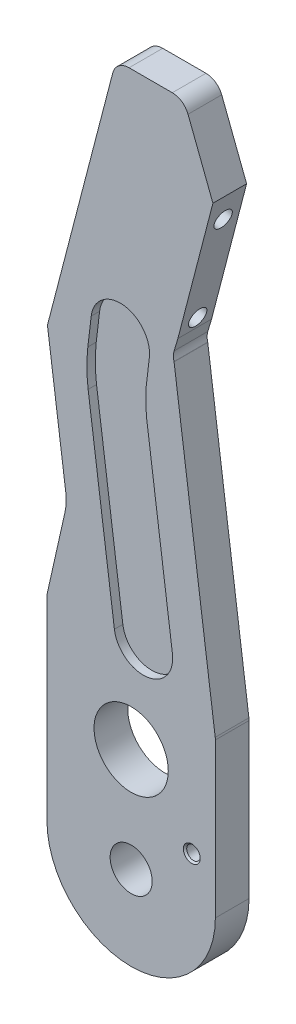
SolidWorks part; units mm, degrees
material "6061-T6 (SS)"
ref_plane "Front Plane" through (0, 0, 0) normal (0, 0, 1) x (1, 0, 0)
ref_plane "Top Plane" through (0, 0, 0) normal (0, 1, 0) x (1, 0, 0)
ref_plane "Right Plane" through (0, 0, 0) normal (1, 0, 0) x (0, 0, -1)
sketch "Sketch1" plane through (0, 0, 0) normal (0, 0, 1) x (1, 0, 0)
  line L0 (-24.2004, 107.4485) -> (-31.75, 73.7706)
  line L2 (-24.2004, 107.4485) -> (-32.7161, 170.4739)
  line L3 (-32.7161, 170.4739) -> (-5.5248, 261.3261)
  line L5 (-31.75, 73.7706) -> (-31.75, 0)
  line L6 (0, 0) -> (0, 372.519) construction
  line L7 (0, 372.519) -> (0, 0) construction
  line L8 (0, 0) -> (0, -96.7447) construction
  line L9 (-31.75, 0) -> (31.75, 0) construction
  line L10 (-108.2097, 215.9) -> (162.3463, 215.9) construction
  line L13 (31.75, 0) -> (31.75, 116.627)
  line L15 (31.9476, 229.9905) -> (19.8752, 261.3261)
  line L16 (19.8752, 261.3261) -> (-5.5248, 261.3261)
  line L17 (31.75, 116.627) -> (15.6763, 175.6244)
  line L18 (15.6763, 175.6244) -> (31.9476, 229.9905)
  arc A0 (-31.75, 0) -> (31.75, 0) centre (0, 0) ccw
  circle A1 centre (0, 0) radius 7.9375
  circle A2 centre (0, 39.116) radius 13.9954
  point P14 (0, -31.75)
  point P23 (-19.1204, 215.9)
  dimension "D1" = 15.875
  dimension "D2" = 27.9908
  dimension "D3" = 31.75
  dimension "D4" = 39.116
  dimension "D5" = 215.9
  dimension "D6" = 94.8339
  dimension "D7" = 25.4
  dimension "D8" = 33.5807
  dimension "D9" = 45.4261
  dimension "D10" = 87.8841
  dimension "D11" = 116.627
  dimension "D12" = 68.1759
  dimension "D13" = 39.8767
  dimension "D14" = 48.3924
  dimension "D15" = 33.6779
  dimension "D16" = 34.5137
extrude "Boss-Extrude1" add sketch "Sketch1" along normal blind 12.7
fillet "Fillet3" radius 19.05 1 edges at (-24.2004, 107.4485, 6.35)
fillet "Fillet1" radius 6.35 7 edges at (-31.75, 73.7706, 6.35) (31.75, 116.627, 6.35) (19.8752, 261.3261, 6.35) (31.9476, 229.9905, 6.35) (-5.5248, 261.3261, 6.35) (-32.7161, 170.4739, 6.35) (15.6763, 175.6244, 6.35)
ref_plane "Plane1" through (0, 261.3261, 0) normal (0, 1, 0) x (1, 0, 0)
ref_plane "Plane2" through (0, 215.9, 0) normal (0, 1, 0) x (1, 0, 0)
ref_plane "Plane3" through (-131.75, 0, 0) normal (-1, 0, 0) x (0, 0, 1)
sketch "Sketch11" plane through (0, 0, 12.7) normal (0, 0, 1) x (1, 0, 0)
  line L0 (-31.75, 7.9375) -> (31.75, 7.9375) construction
  line L1 (-31.75, 73.7706) -> (-31.75, 0) construction
  line L2 (31.75, 0) -> (31.75, 116.627) construction
  line L3 (-31.75, 25.1206) -> (31.75, 25.1206) construction
  line L5 (0, 25.1206) -> (0, 7.9375) construction
  line L7 (-31.75, 16.529) -> (31.75, 16.529) construction
  line L9 (22.86, 25.1206) -> (22.86, 7.9375) construction
  circle A0 centre (0, 0) radius 7.9375 construction
  circle A2 centre (0, 39.116) radius 13.9954 construction
  point P6 (0, 7.9375)
  point P11 (0, 25.1206)
  point P24 (0, 16.529)
  point P30 (22.86, 16.529)
  dimension "D1" = 8.89
hole_wizard "#10 Clearance Hole2" positions "Sketch11" profile "Sketch13" hole size "#10" standard "ANSI Inch" end condition through all
sketch "Sketch13" plane through (22.86, 16.529, 12.7) normal (1, 0, 0) x (0, -1, 0)
  line L0 (0, 0) -> (0, 12.7)
  line L1 (0, 12.7) -> (2.5527, 12.7)
  line L2 (2.5527, 12.7) -> (2.5527, 0.635)
  line L3 (2.5527, 0.635) -> (3.1877, 0)
  line L5 (3.1877, 0) -> (0, 0)
  line L6 (-2.5527, 0.635) -> (-3.1877, 0) construction
  line L11 (0, -6.35) -> (0, 107.95) construction
  dimension "Thru Hole Dia." = 5.1054
  dimension "Thru Hole Depth" = 12.7
  dimension "Near C'Sink Dia." = 6.3754
  dimension "Near C'Sink Angle" = 90
sketch "Sketch15" plane through (-76.8533, 23.0015, 0) normal (-0.958, 0.2867, 0) x (0, 0, 1)
  line L0 (-81.5042, 201.3527) -> (87.1801, 201.3527) construction
sketch "Sketch17" plane through (0, 0, 0) normal (0, 0, -1) x (-1, 0, 0)
  line L0 (-15.9306, 175.6213) -> (-31.75, 58.5394)
  line L1 (-31.75, 0) -> (-31.75, 115.7775) construction
  line L2 (32.5326, 169.1159) -> (24.6578, 110.8333) construction
  line L12 (31.75, 0) -> (31.75, 73.0675)
  line L13 (31.5962, 74.4566) -> (24.9476, 104.1156)
  line L14 (24.6578, 110.8333) -> (32.5326, 169.1159)
  line L15 (32.3231, 171.7868) -> (6.8804, 256.7968)
  line L16 (0.797, 261.3261) -> (-15.5167, 261.3261)
  line L17 (-21.4421, 257.2589) -> (-31.1675, 232.0153)
  line L18 (-31.3254, 227.9117) -> (-16.1967, 177.3632)
  line L19 (-16.1534, 173.8733) -> (-31.5267, 117.4467)
  line L20 (-31.75, 115.7775) -> (-31.75, 0)
  line L21 (31.75, 0) -> (31.75, 73.0675)
  line L22 (31.5962, 74.4566) -> (24.9476, 104.1156)
  line L23 (24.6578, 110.8333) -> (32.5326, 169.1159)
  line L24 (32.3231, 171.7868) -> (6.8804, 256.7968)
  line L25 (0.797, 261.3261) -> (-15.5167, 261.3261)
  line L26 (-21.4421, 257.2589) -> (-31.1675, 232.0153)
  line L27 (-31.3254, 227.9117) -> (-16.1967, 177.3632)
  line L28 (-16.1534, 173.8733) -> (-31.5267, 117.4467)
  line L29 (-31.75, 115.7775) -> (-31.75, 0)
  arc A0 (-16.1534, 173.8733) -> (-16.1967, 177.3632) centre (-22.2801, 175.5425) ccw construction
  arc A10 (31.75, 73.0675) -> (31.5962, 74.4566) centre (25.4, 73.0675) ccw
  arc A11 (24.6578, 110.8333) -> (24.9476, 104.1156) centre (43.5362, 108.2826) ccw
  arc A12 (32.5326, 169.1159) -> (32.3231, 171.7868) centre (26.2398, 169.9661) ccw
  arc A13 (6.8804, 256.7968) -> (0.797, 261.3261) centre (0.797, 254.9761) ccw
  arc A14 (-15.5167, 261.3261) -> (-21.4421, 257.2589) centre (-15.5167, 254.9761) ccw
  arc A15 (-31.1675, 232.0153) -> (-31.3254, 227.9117) centre (-25.2421, 229.7324) ccw
  arc A16 (-16.1534, 173.8733) -> (-16.1967, 177.3632) centre (-22.2801, 175.5425) ccw
  arc A17 (-31.5267, 117.4467) -> (-31.75, 115.7775) centre (-25.4, 115.7775) ccw
  arc A18 (-31.75, 0) -> (31.75, 0) centre (0, 0) ccw
  arc A19 (31.75, 73.0675) -> (31.5962, 74.4566) centre (25.4, 73.0675) ccw
  arc A21 (32.5326, 169.1159) -> (32.3231, 171.7868) centre (26.2398, 169.9661) ccw
  arc A22 (6.8804, 256.7968) -> (0.797, 261.3261) centre (0.797, 254.9761) ccw
  arc A23 (-15.5167, 261.3261) -> (-21.4421, 257.2589) centre (-15.5167, 254.9761) ccw
  arc A24 (-31.1675, 232.0153) -> (-31.3254, 227.9117) centre (-25.2421, 229.7324) ccw
  arc A25 (-16.1534, 173.8733) -> (-16.1967, 177.3632) centre (-22.2801, 175.5425) ccw
  arc A26 (-31.5267, 117.4467) -> (-31.75, 115.7775) centre (-25.4, 115.7775) ccw
  arc A27 (-31.75, 0) -> (31.75, 0) centre (0, 0) ccw
  arc A28 (24.6578, 110.8333) -> (24.9476, 104.1156) centre (43.5362, 108.2826) ccw
  line M35 (-16.1534, 173.8733) -> (-31.5267, 117.4467)
  arc M36 (-31.5267, 117.4467) -> (-31.75, 115.7775) centre (-25.4, 115.7775) ccw
  line M37 (-31.75, 115.7775) -> (-31.75, 0)
  dimension "D1" = 0
extrude "Cut-Extrude1" cut sketch "Sketch17" against normal through all both and the other way through all contours L0 M35 M36 M37
fillet "Fillet2" radius 6.35 1 edges at (31.75, 58.5394, 6.35)
sketch "Sketch18" plane through (0, 0, 12.7) normal (0, 0, 1) x (1, 0, 0)
  line L0 (-32.3231, 171.7868) -> (16.4487, 171.7868) construction
  line L1 (16.1799, 173.7761) -> (31.6928, 58.9626) construction
  line L2 (-6.8804, 256.7968) -> (30.8434, 256.7968) construction
sketch "Sketch19" plane through (0, 0, 0) normal (0, 0, -1) x (-1, 0, 0)
  line L0 (6.8804, 256.7968) -> (31.5572, 161.8973)
  line L1 (32.5326, 169.1159) -> (24.6578, 110.8333) construction
  line L2 (-15.9306, 175.6213) -> (-30.8256, 232.9028)
  line L3 (-31.1675, 232.0153) -> (-21.4421, 257.2589) construction
  line L4 (31.75, 73.0675) -> (31.75, 0) construction
  line L14 (-16.1799, 173.7761) -> (-31.6928, 58.9626)
  line L15 (-31.75, 58.1123) -> (-31.75, 0)
  line L16 (31.75, 0) -> (31.75, 73.0675)
  line L17 (31.5962, 74.4566) -> (24.9476, 104.1156)
  line L18 (24.6578, 110.8333) -> (32.5326, 169.1159)
  line L19 (32.3231, 171.7868) -> (6.8804, 256.7968)
  line L20 (0.797, 261.3261) -> (-15.5167, 261.3261)
  line L21 (-21.4421, 257.2589) -> (-31.1675, 232.0153)
  line L22 (-31.3254, 227.9117) -> (-16.1967, 177.3632)
  line L23 (-16.1534, 173.8733) -> (-16.1799, 173.7761)
  line L24 (-16.1799, 173.7761) -> (-31.6928, 58.9626)
  line L25 (-31.75, 58.1123) -> (-31.75, 0)
  line L26 (31.75, 0) -> (31.75, 73.0675)
  line L27 (31.5962, 74.4566) -> (24.9476, 104.1156)
  line L28 (24.6578, 110.8333) -> (32.5326, 169.1159)
  line L29 (32.3231, 171.7868) -> (6.8804, 256.7968)
  line L30 (0.797, 261.3261) -> (-15.5167, 261.3261)
  line L31 (-21.4421, 257.2589) -> (-31.1675, 232.0153)
  line L32 (-31.3254, 227.9117) -> (-16.1967, 177.3632)
  line L33 (-16.1534, 173.8733) -> (-16.1799, 173.7761)
  arc A0 (-16.1534, 173.8733) -> (-16.1967, 177.3632) centre (-22.2801, 175.5425) ccw construction
  arc A10 (-31.6928, 58.9626) -> (-31.75, 58.1123) centre (-25.4, 58.1123) ccw
  arc A11 (-31.75, 0) -> (31.75, 0) centre (0, 0) ccw
  arc A12 (31.75, 73.0675) -> (31.5962, 74.4566) centre (25.4, 73.0675) ccw
  arc A13 (24.6578, 110.8333) -> (24.9476, 104.1156) centre (43.5362, 108.2826) ccw
  arc A14 (32.5326, 169.1159) -> (32.3231, 171.7868) centre (26.2398, 169.9661) ccw
  arc A15 (6.8804, 256.7968) -> (0.797, 261.3261) centre (0.797, 254.9761) ccw
  arc A16 (-15.5167, 261.3261) -> (-21.4421, 257.2589) centre (-15.5167, 254.9761) ccw
  arc A17 (-31.1675, 232.0153) -> (-31.3254, 227.9117) centre (-25.2421, 229.7324) ccw
  arc A18 (-16.1534, 173.8733) -> (-16.1967, 177.3632) centre (-22.2801, 175.5425) ccw
  arc A19 (-31.6928, 58.9626) -> (-31.75, 58.1123) centre (-25.4, 58.1123) ccw
  arc A20 (-31.75, 0) -> (31.75, 0) centre (0, 0) ccw
  arc A21 (31.75, 73.0675) -> (31.5962, 74.4566) centre (25.4, 73.0675) ccw
  arc A23 (32.5326, 169.1159) -> (32.3231, 171.7868) centre (26.2398, 169.9661) ccw
  arc A24 (6.8804, 256.7968) -> (0.797, 261.3261) centre (0.797, 254.9761) ccw
  arc A25 (-15.5167, 261.3261) -> (-21.4421, 257.2589) centre (-15.5167, 254.9761) ccw
  arc A26 (-31.1675, 232.0153) -> (-31.3254, 227.9117) centre (-25.2421, 229.7324) ccw
  arc A27 (-16.1534, 173.8733) -> (-16.1967, 177.3632) centre (-22.2801, 175.5425) ccw
  arc A28 (24.6578, 110.8333) -> (24.9476, 104.1156) centre (43.5362, 108.2826) ccw
  line M33 (24.6578, 110.8333) -> (32.5326, 169.1159)
  arc M34 (32.5326, 169.1159) -> (32.3231, 171.7868) centre (26.2398, 169.9661) ccw
  line M35 (32.3231, 171.7868) -> (6.8804, 256.7968)
  line M39 (-21.4421, 257.2589) -> (-31.1675, 232.0153)
  arc M40 (-31.1675, 232.0153) -> (-31.3254, 227.9117) centre (-25.2421, 229.7324) ccw
  line M41 (-31.3254, 227.9117) -> (-16.1967, 177.3632)
  dimension "D1" = 0
  dimension "D2" = 94.8994
  dimension "D3" = 144.354
  dimension "D4" = 0.1928
extrude "Cut-Extrude3" cut sketch "Sketch19" against normal through all both and the other way through all contours L2 M41 M39 M40 | L0 M35 M33 M34
sketch "Sketch20" plane through (-68.9908, 17.9398, 0) normal (-0.9678, 0.2517, 0) x (0, 0, 1)
  line L0 (6.35, 148.7449) -> (6.35, 246.8002) construction
  line L1 (12.7, 148.7449) -> (0, 148.7449) construction
  line L2 (12.7, 246.8002) -> (0, 246.8002) construction
  line L3 (-81.5042, 204.1394) -> (87.1801, 204.1394) construction
  line L4 (-81.5042, 204.1394) -> (87.1801, 204.1394) construction
  point P6 (6.35, 223.1894)
  point P11 (6.35, 185.0894)
  dimension "D1" = 19.05
hole_wizard "1/4 Clearance Hole1" positions "Sketch20" profile "Sketch21" hole size "1/4" standard "ANSI Inch" end condition through all
sketch "Sketch21" plane through (-22.4107, 197.0721, 6.35) normal (0, 0, 1) x (-0.2517, -0.9678, 0)
  line L0 (0, 0) -> (0, 110.0035)
  line L1 (0, 110.0035) -> (3.3782, 110.0035)
  line L2 (3.3782, 110.0035) -> (3.3782, 0.635)
  line L3 (3.3782, 0.635) -> (4.0132, 0)
  line L5 (4.0132, 0) -> (0, 0)
  line L6 (-3.3782, 0.635) -> (-4.0132, 0) construction
  line L11 (0, -6.35) -> (0, 107.95) construction
  dimension "Thru Hole Dia." = 6.7564
  dimension "Thru Hole Depth" = 110.0035
  dimension "Near C'Sink Dia." = 8.0264
  dimension "Near C'Sink Angle" = 90
sketch "Sketch22" plane through (0, 0, 0) normal (0, 0, -1) x (-1, 0, 0)
  line L0 (32.3231, 171.7868) -> (-16.4487, 171.7868) construction
  line L3 (-20.6308, 140.834) -> (27.8267, 134.2867) construction
  line L4 (-16.1799, 173.7761) -> (-31.6928, 58.9626) construction
  line L5 (31.5572, 161.8973) -> (24.6578, 110.8333) construction
  line L6 (-4.6234, 76.7135) -> (5.2868, 150.0599) construction
  line L7 (-15.5639, 78.1918) -> (-5.6538, 151.5381)
  line L8 (6.3172, 75.2353) -> (16.2274, 148.5817)
  line L9 (-15.5167, 261.3261) -> (0.797, 261.3261) construction
  line L10 (4.1046, 171.7868) -> (5.3755, 161.085) construction
  line L11 (15.0675, 173.0888) -> (16.3385, 162.387)
  line L12 (-6.8584, 170.4849) -> (-5.5874, 159.7831)
  line L13 (6.8804, 256.7968) -> (31.5572, 161.8973) construction
  line L14 (-24.2233, 207.5123) -> (16.9143, 218.2094) construction
  line L15 (-30.8256, 232.9028) -> (-17.6209, 182.1219) construction
  line L16 (-31.75, 0) -> (-31.75, 58.1123) construction
  arc A5 (-15.5639, 78.1918) -> (6.3172, 75.2353) centre (-4.6234, 76.7135) ccw
  arc A6 (16.2274, 148.5817) -> (-5.6538, 151.5381) centre (5.2868, 150.0599) ccw
  arc A7 (15.0675, 173.0888) -> (-6.8584, 170.4849) centre (4.1046, 171.7868) ccw
  arc A8 (-5.5874, 159.7831) -> (16.3385, 162.387) centre (5.3755, 161.085) ccw
  arc A10 (16.3385, 162.387) -> (16.2274, 148.5817) centre (-38.0995, 155.922) cw
  arc A11 (-5.6471, 160.2856) -> (-5.7215, 151.0366) centre (-146.3113, 156.7929) cw
  point P2 (0.3317, 113.3867)
  point P13 (3.5979, 137.5604)
  point P14 (4.74, 166.4359)
  point P15 (6.765, 161.0005)
  dimension "D3" = 100.3256
  dimension "D6" = 24.8916
  dimension "D4" = 140.7075
  dimension "D5" = 54.8205
  dimension "D1" = 22.08
  dimension "D2" = 74.0128
  dimension "D9" = 58.1123
extrude "Cut-Extrude4" cut sketch "Sketch22" against normal blind 3.175 contours A8 A6 L7 A5 L8 | A6 A8 | L12 A8 A6 L11 A7 | A10 A8 A6 | L12 A11 L7 A6 A8
sketch "Sketch23" plane through (0, 0, 12.7) normal (0, 0, 1) x (1, 0, 0)
  line L2 (15.5639, 78.1918) -> (5.6538, 151.5381)
  line L3 (-16.2274, 148.5817) -> (-6.3172, 75.2353)
  line L4 (15.5639, 78.1918) -> (5.6538, 151.5381)
  line L5 (-16.2274, 148.5817) -> (-6.3172, 75.2353)
  line L6 (-15.0675, 173.0888) -> (-16.3385, 162.387)
  line L7 (5.5874, 159.7831) -> (6.8584, 170.4849)
  line L8 (-15.0675, 173.0888) -> (-16.3385, 162.387)
  line L9 (5.5874, 159.7831) -> (6.8584, 170.4849)
  arc A0 (-16.3385, 162.387) -> (-16.2274, 148.5817) centre (38.0995, 155.922) ccw construction
  arc A1 (5.6471, 160.2856) -> (5.7215, 151.0366) centre (146.3113, 156.7929) ccw construction
  arc A2 (5.6538, 151.5381) -> (-16.2274, 148.5817) centre (-5.2868, 150.0599) ccw
  arc A3 (-6.3172, 75.2353) -> (15.5639, 78.1918) centre (4.6234, 76.7135) ccw
  arc A4 (5.6538, 151.5381) -> (-16.2274, 148.5817) centre (-5.2868, 150.0599) ccw
  arc A5 (-6.3172, 75.2353) -> (15.5639, 78.1918) centre (4.6234, 76.7135) ccw
  arc A6 (-16.3385, 162.387) -> (5.5874, 159.7831) centre (-5.3755, 161.085) ccw
  arc A7 (6.8584, 170.4849) -> (-15.0675, 173.0888) centre (-4.1046, 171.7868) ccw
  arc A8 (-16.3385, 162.387) -> (5.5874, 159.7831) centre (-5.3755, 161.085) ccw
  arc A9 (6.8584, 170.4849) -> (-15.0675, 173.0888) centre (-4.1046, 171.7868) ccw
  arc A10 (-16.3385, 162.387) -> (-16.2274, 148.5817) centre (38.0995, 155.922) ccw
  arc A11 (5.6471, 160.2856) -> (5.7215, 151.0366) centre (146.3113, 156.7929) ccw
  dimension "D1" = 0
  dimension "D2" = 0
extrude "Cut-Extrude5" cut sketch "Sketch23" against normal blind 3.175 contours A8 A4 L5 A5 L4 | A4 A8 | L9 A9 L8 A8 A4 | A8 A10 A4 | A11 L9 A8 A4 L4
ref_plane "Plane4" through (0, 261.3261, 0) normal (0, 1, 0) x (1, 0, 0)
ref_plane "Plane5" through (0, -31.75, 0) normal (0, -1, 0) x (-1, 0, 0)
ref_plane "Plane6" through (-31.75, 0, 0) normal (-1, 0, 0) x (0, 0, 1)
ref_plane "Plane7" through (30.8256, 0, 0) normal (-1, 0, 0) x (0, 0, 1)
